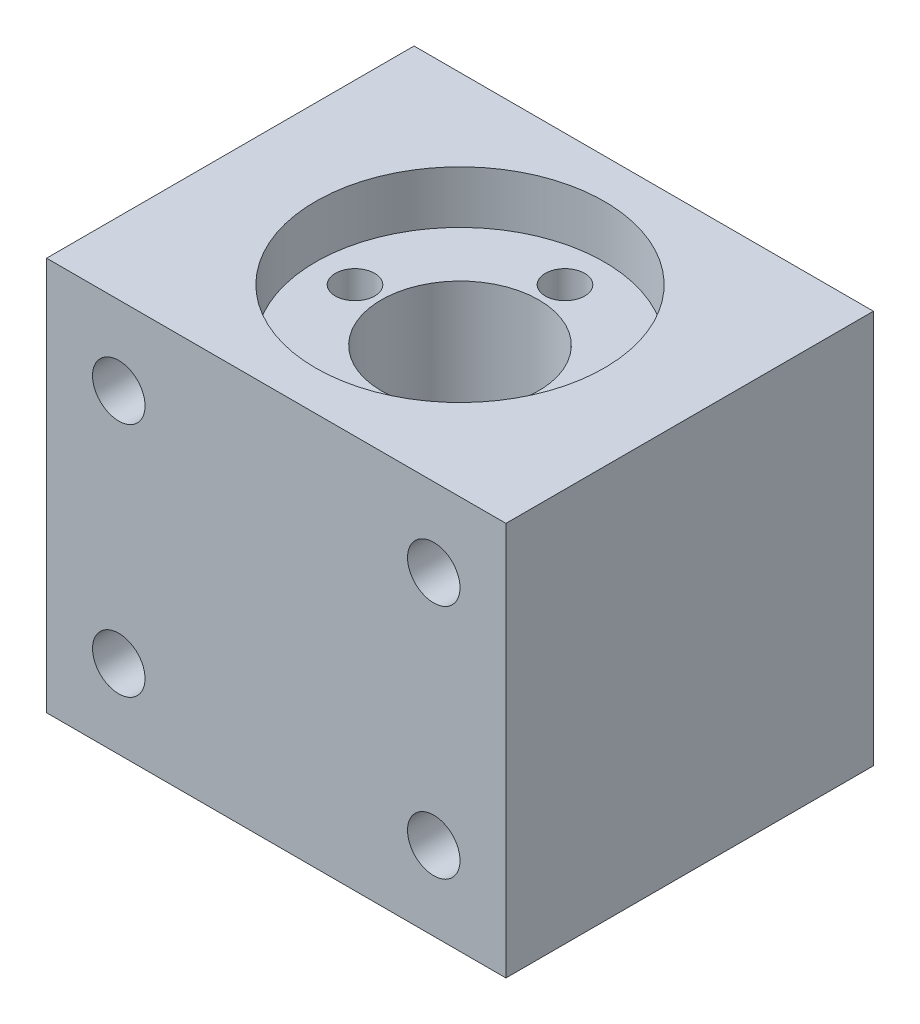
SolidWorks part; units mm, degrees
ref_plane "Front Plane" through (0, 0, 0) normal (0, 0, 1) x (1, 0, 0)
ref_plane "Top Plane" through (0, 0, 0) normal (0, 1, 0) x (1, 0, 0)
ref_plane "Right Plane" through (0, 0, 0) normal (1, 0, 0) x (0, 0, -1)
sketch "Sketch1" plane through (0, 0, 0) normal (0, 0, 1) x (1, 0, 0)
  line L1 (0, 0) -> (35, 0)
  line L2 (0, 0) -> (0, 30)
  line L3 (0, 30) -> (35, 30)
  line L4 (35, 0) -> (35, 30)
extrude "Boss-Extrude1" add sketch "Sketch1" along normal blind 28
sketch "Sketch2" plane through (0, 0, 28) normal (0, 0, 1) x (1, 0, 0)
  circle A0 centre (5.5, 24) radius 2
  circle A1 centre (5.5, 6) radius 2
  circle A2 centre (29.5, 6) radius 2
  circle A3 centre (29.5, 24) radius 2
extrude "Cut-Extrude1" cut sketch "Sketch2" against normal blind 7
sketch "Sketch4" plane through (0, 0, 0) normal (0, -1, 0) x (1, 0, 0)
  circle A0 centre (17.5, 14) radius 7
extrude "Cut-Extrude2" cut sketch "Sketch4" against normal blind 8
sketch "Sketch5" plane through (0, 8, 0) normal (0, -1, 0) x (-1, 0, 0)
  circle A0 centre (-17.5, -14) radius 6
extrude "Cut-Extrude3" cut sketch "Sketch5" against normal blind 50
sketch "Sketch6" plane through (0, 30, 0) normal (0, 1, 0) x (1, 0, 0)
  circle A0 centre (17.5, -14) radius 11
extrude "Cut-Extrude4" cut sketch "Sketch6" against normal blind 4
sketch "Sketch7" plane through (0, 26, 0) normal (0, 1, 0) x (1, 0, 0)
  circle A0 centre (17.5, -6) radius 1.5
  circle A1 centre (9.5, -14) radius 1.5
  circle A2 centre (17.5, -22) radius 1.5
  circle A3 centre (25.5, -14) radius 1.5
extrude "Cut-Extrude5" cut sketch "Sketch7" against normal blind 10
sketch "Sketch8" plane through (0, 0, 0) normal (0, 0, -1) x (-1, 0, 0)
  circle A0 centre (-5, 15) radius 1.5
extrude "Cut-Extrude6" cut sketch "Sketch8" against normal blind 10
